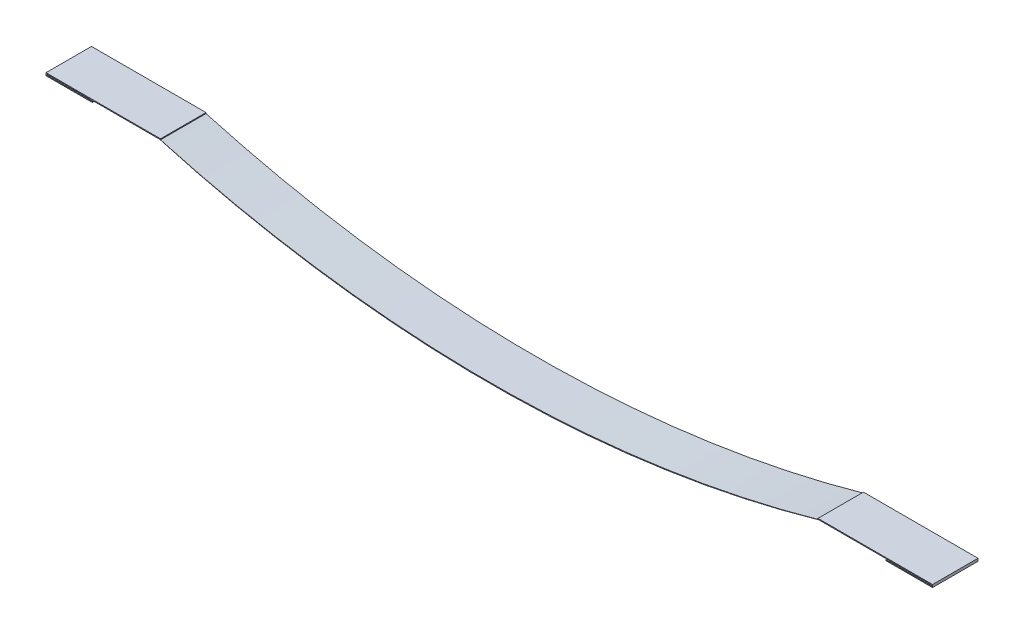
SolidWorks part; units mm, degrees
ref_plane "Front Plane" through (0, 0, 0) normal (0, 0, 1) x (1, 0, 0)
ref_plane "Top Plane" through (0, 0, 0) normal (0, 1, 0) x (1, 0, 0)
ref_plane "Right Plane" through (0, 0, 0) normal (1, 0, 0) x (0, 0, -1)
sketch "Sketch1" plane through (0, 0, 0) normal (0, 0, 1) x (1, 0, 0)
  line L0 (-443.5, 0) -> (-368.3, 0) construction
  line L1 (-444.5, 0) -> (-494.3, 0)
  line L2 (-494.3, 0) -> (-494.3, -1)
  line L3 (-494.3, -1) -> (-444.5, -1)
  line L4 (-444.5, -1) -> (-444.5, 0)
  line L5 (-444.5, 0) -> (-444.5, 1) construction
  line L6 (-444.5, 1) -> (-495.3, 1)
  line L7 (-495.3, 1) -> (-495.3, -2)
  line L8 (-495.3, -2) -> (-444.5, -2)
  line L9 (-444.5, -1) -> (-444.5, -2) construction
  line L10 (-444.5, 1) -> (-368.3, 1)
  line L11 (-368.3, 1) -> (-368.3, 0) construction
  line L12 (-368.3, 0) -> (-443.5, 0)
  line L13 (-494.3, -0.5) -> (-495.3, -0.5) construction
  line L14 (-444.5, -2) -> (-443.5, -2)
  line L15 (-443.5, -2) -> (-443.5, 0)
  line L17 (0, 0) -> (0, -50.8) construction
  line L18 (-368.3, 1) -> (-367.3, 1)
  line L19 (-367.3, 1) -> (-367.3, 0)
  line L20 (0, -50.8) -> (0, -51.8) construction
  line L21 (-368.3, 0) -> (-367.3, 0) construction
  line L22 (-367.3, 0) -> (367.3, 0) construction
  line L23 (368.3, 0) -> (367.3, 0) construction
  line L24 (444.5, 0) -> (443.5, 0) construction
  line L25 (494.3, -0.5) -> (495.3, -0.5) construction
  line L26 (443.5, 0) -> (368.3, 0) construction
  line L27 (367.3, 1) -> (367.3, 0)
  line L28 (368.3, 1) -> (367.3, 1)
  line L29 (443.5, -2) -> (443.5, 0)
  line L30 (444.5, -2) -> (443.5, -2)
  line L31 (368.3, 0) -> (443.5, 0)
  line L32 (368.3, 1) -> (368.3, 0) construction
  line L33 (444.5, 1) -> (368.3, 1)
  line L34 (444.5, -1) -> (444.5, -2) construction
  line L35 (495.3, -2) -> (444.5, -2)
  line L36 (495.3, 1) -> (495.3, -2)
  line L37 (444.5, 1) -> (495.3, 1)
  line L38 (444.5, 0) -> (444.5, 1) construction
  line L39 (444.5, -1) -> (444.5, 0)
  line L40 (494.3, -1) -> (444.5, -1)
  line L41 (494.3, 0) -> (494.3, -1)
  line L42 (444.5, 0) -> (494.3, 0)
  line L43 (367.3, 0) -> (361.2938, 0) construction
  line L44 (367.3, 0) -> (367.3, 1) construction
  arc A0 (-368.3, 0) -> (368.3, 0) centre (0, 1283.4136) ccw
  arc A1 (-367.3, 0) -> (367.3, 0) centre (0, 1302.4473) ccw
  point P3 (0, 0)
  point P4 (0, 0)
  point P19 (-406.6674, -2.0351)
  point P23 (0, -51.8)
  dimension "D1" = 1
  dimension "D2" = 76.2
  dimension "D3" = 50.8
  dimension "D4" = 495.3
  dimension "D5" = 50.8
extrude "Boss-Extrude1" add sketch "Sketch1" along normal blind 50.8
